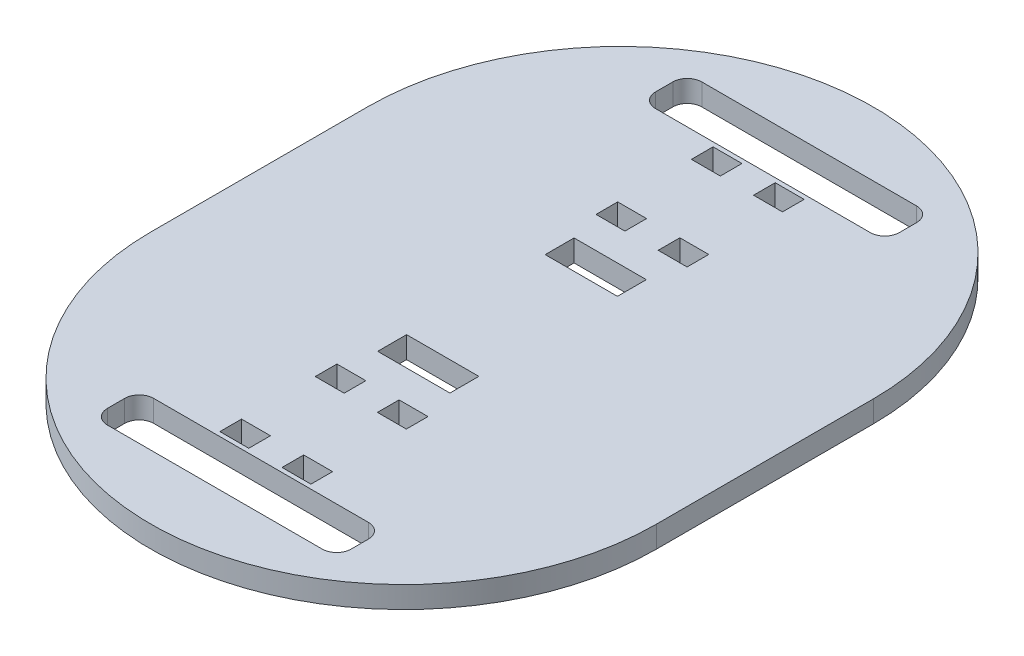
SolidWorks part; units mm, degrees
ref_plane "Front Plane" through (0, 0, 0) normal (0, 0, 1) x (1, 0, 0)
ref_plane "Top Plane" through (0, 0, 0) normal (0, 1, 0) x (1, 0, 0)
ref_plane "Right Plane" through (0, 0, 0) normal (1, 0, 0) x (0, 0, -1)
sketch "Sketch1" plane through (0, 0, 0) normal (0, 1, 0) x (1, 0, 0)
  line L0 (0, 0) -> (0, 76.2) construction
  line L1 (-88.9, 0) -> (-88.9, 76.2)
  line L2 (88.9, 0) -> (88.9, 76.2)
  arc A0 (-88.9, 0) -> (88.9, 0) centre (0, 0) ccw
  arc A1 (88.9, 76.2) -> (-88.9, 76.2) centre (0, 76.2) ccw
  point P3 (0, 38.1)
  dimension "D2" = 88.9
  dimension "D1" = 76.2
extrude "Boss-Extrude1" add sketch "Sketch1" along normal blind 7.62 contours A1 L1 A0 L2
sketch "Sketch2" plane through (0, 7.62, 0) normal (0, 1, 0) x (1, 0, 0)
  line L0 (0, 165.1) -> (0, -88.9) construction
  line L1 (-67.1704, 134.4352) -> (67.1704, 134.4352) construction
  line L3 (-67.1704, -58.2352) -> (67.1704, -58.2352) construction
  line L4 (-42.8387, -66.3632) -> (42.8387, -66.3632)
  line L5 (-42.8387, -66.3632) -> (-42.8387, -50.1072)
  line L6 (-42.8387, -50.1072) -> (42.8387, -50.1072)
  line L7 (42.8387, -66.3632) -> (42.8387, -50.1072)
  line L8 (-42.8387, -66.3632) -> (42.8387, -50.1072) construction
  line L9 (-42.8387, -50.1072) -> (42.8387, -66.3632) construction
  line L15 (-88.9, 38.1) -> (88.9, 38.1) construction
  line L16 (-88.9, 0) -> (-88.9, 76.2) construction
  line L17 (88.9, 0) -> (88.9, 76.2) construction
  line L18 (-42.8387, 142.5632) -> (42.8387, 126.3072) construction
  line L19 (-67.1704, 134.4352) -> (67.1704, 134.4352) construction
  line L20 (-42.8387, 126.3072) -> (42.8387, 142.5632) construction
  line L21 (42.8387, 142.5632) -> (42.8387, 126.3072)
  line L22 (-42.8387, 126.3072) -> (42.8387, 126.3072)
  line L23 (-42.8387, 142.5632) -> (-42.8387, 126.3072)
  line L24 (-42.8387, 142.5632) -> (42.8387, 142.5632)
  arc A0 (88.9, 76.2) -> (-88.9, 76.2) centre (0, 76.2) ccw construction
  arc A1 (-88.9, 0) -> (88.9, 0) centre (0, 0) ccw construction
  point P10 (0, -58.2352)
  dimension "D1" = 16.256
extrude "Cut-Extrude1" cut sketch "Sketch2" against normal through all and the other way through all contours L6 L7 L4 L5 | L22 L21 L24 L23
fillet "Fillet1" radius 5.08 8 edges at (-42.8387, 3.81, -142.5632) (-42.8387, 3.81, -126.3072) (42.8387, 3.81, -142.5632) (42.8387, 3.81, -126.3072) (42.8387, 3.81, 50.1072) (42.8387, 3.81, 66.3632) (-42.8387, 3.81, 66.3632) (-42.8387, 3.81, 50.1072)
sketch "Sketch3" plane through (0, 7.62, 0) normal (0, 1, 0) x (1, 0, 0)
  line L0 (-42.8387, 134.4352) -> (42.8387, 134.4352) construction
  line L1 (-42.8387, 137.4832) -> (-42.8387, 131.3872) construction
  line L2 (42.8387, 137.4832) -> (42.8387, 131.3872) construction
  line L3 (0, 134.4352) -> (0, 83.6352) construction
  line L4 (-16.002, 83.6352) -> (16.002, 83.6352)
  line L5 (16.002, 91.2552) -> (16.002, 134.4352) construction
  line L10 (-16.002, 83.6352) -> (-5.842, 83.6352)
  line L11 (-16.002, 83.6352) -> (-16.002, 91.2552)
  line L12 (-16.002, 91.2552) -> (-5.842, 91.2552)
  line L13 (-5.842, 83.6352) -> (-5.842, 91.2552)
  line L14 (16.002, 83.6352) -> (5.842, 83.6352)
  line L15 (16.002, 83.6352) -> (16.002, 91.2552)
  line L16 (16.002, 91.2552) -> (5.842, 91.2552)
  line L17 (5.842, 83.6352) -> (5.842, 91.2552)
  line L18 (-16.002, 91.2552) -> (-16.002, 134.4352) construction
  line L19 (16.002, 134.4352) -> (16.002, 124.7832) construction
  line L20 (16.002, 117.1632) -> (-16.002, 117.1632) construction
  line L21 (16.002, 124.7832) -> (5.842, 124.7832)
  line L22 (16.002, 124.7832) -> (16.002, 117.1632)
  line L23 (16.002, 117.1632) -> (5.842, 117.1632)
  line L24 (5.842, 124.7832) -> (5.842, 117.1632)
  line L25 (-16.002, 124.7832) -> (-5.842, 124.7832)
  line L26 (-16.002, 124.7832) -> (-16.002, 117.1632)
  line L27 (-16.002, 117.1632) -> (-5.842, 117.1632)
  line L28 (-5.842, 124.7832) -> (-5.842, 117.1632)
  line L29 (-88.9, 38.1) -> (88.9, 38.1) construction
  line L30 (-88.9, 0) -> (-88.9, 76.2) construction
  line L31 (88.9, 0) -> (88.9, 76.2) construction
  line L32 (16.002, -15.0552) -> (5.842, -15.0552)
  line L33 (5.842, -7.4352) -> (5.842, -15.0552)
  line L34 (16.002, -7.4352) -> (5.842, -7.4352)
  line L35 (16.002, -7.4352) -> (16.002, -15.0552)
  line L36 (-16.002, -15.0552) -> (-5.842, -15.0552)
  line L37 (-5.842, -7.4352) -> (-5.842, -15.0552)
  line L38 (-16.002, -7.4352) -> (-5.842, -7.4352)
  line L39 (-16.002, -7.4352) -> (-16.002, -15.0552)
  line L40 (16.002, -40.9632) -> (5.842, -40.9632)
  line L41 (5.842, -48.5832) -> (5.842, -40.9632)
  line L42 (16.002, -48.5832) -> (5.842, -48.5832)
  line L43 (16.002, -48.5832) -> (16.002, -40.9632)
  line L44 (-16.002, -40.9632) -> (-5.842, -40.9632)
  line L45 (-5.842, -48.5832) -> (-5.842, -40.9632)
  line L46 (-16.002, -48.5832) -> (-5.842, -48.5832)
  line L47 (-16.002, -48.5832) -> (-16.002, -40.9632)
  line L48 (42.8387, -58.2352) -> (-42.8387, -58.2352) construction
  line L49 (42.8387, -61.2832) -> (42.8387, -55.1872) construction
  line L50 (-42.8387, -61.2832) -> (-42.8387, -55.1872) construction
  point P12 (0, 83.6352)
  dimension "D1" = 50.8
  dimension "D2" = 32.004
  dimension "D3" = 7.62
  dimension "D4" = 7.62
  dimension "D5" = 9.652
  dimension "D6" = 7.62
  dimension "D7" = 7.62
  dimension "D8" = 0
  dimension "D9" = 9.652
extrude "Cut-Extrude2" cut sketch "Sketch3" against normal through all contours L17 L4 L15 L16 | L4 L13 L12 L11 | L22 L21 L24 L23 | L26 L25 L28 L27 | L36 L37 L38 L39 | L32 L33 L34 L35 | L44 L45 L46 L47 | L40 L41 L42 L43
sketch "Sketch4" plane through (0, 7.62, 0) normal (0, 1, 0) x (1, 0, 0)
  line L0 (-5.842, 83.6352) -> (5.842, 83.6352) construction
  line L1 (5.842, 83.6352) -> (5.842, 73.4752) construction
  line L2 (-12.7, 62.4579) -> (-12.7, 72.6179)
  line L3 (0, 83.6352) -> (0, 67.5379) construction
  line L4 (-12.7, 62.4579) -> (12.7, 62.4579)
  line L5 (-12.7, 72.6179) -> (12.7, 72.6179)
  line L6 (12.7, 62.4579) -> (12.7, 72.6179)
  line L7 (-12.7, 62.4579) -> (12.7, 72.6179) construction
  line L8 (-12.7, 72.6179) -> (12.7, 62.4579) construction
  line L11 (-88.9, 38.1) -> (88.9, 38.1) construction
  line L12 (-88.9, 0) -> (-88.9, 76.2) construction
  line L13 (88.9, 0) -> (88.9, 76.2) construction
  line L14 (-12.7, 13.7421) -> (12.7, 13.7421)
  line L15 (-12.7, 13.7421) -> (-12.7, 3.5821)
  line L16 (-12.7, 3.5821) -> (12.7, 3.5821)
  line L17 (12.7, 13.7421) -> (12.7, 3.5821)
  dimension "D1" = 10.16
  dimension "D2" = 10.16
  dimension "D3" = 25.4
extrude "Cut-Extrude3" cut sketch "Sketch4" against normal through all
equation "\"D1@Boss-Extrude1\"=\"MDF\""
equation "\"MDF\" = 0.3in"
equation "\"D3@Sketch3\"=\"MDF\""
equation "\"D4@Sketch3\"=\"MDF\""
equation "\"D6@Sketch3\"=\"MDF\""
